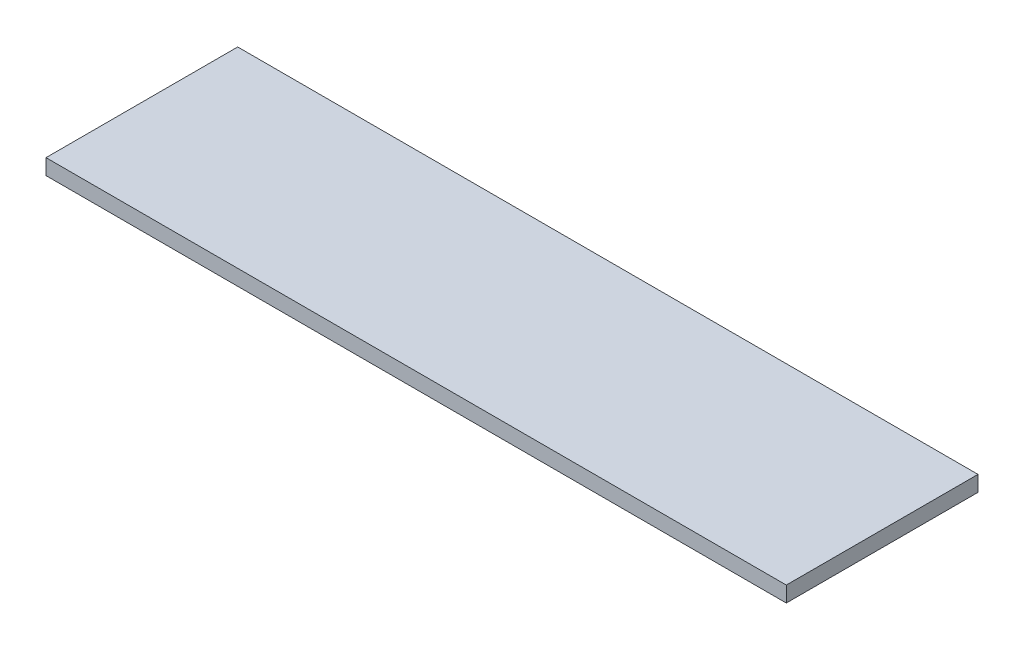
SolidWorks part; units mm, degrees
ref_plane "Front Plane" through (0, 0, 0) normal (0, 0, 1) x (1, 0, 0)
ref_plane "Top Plane" through (0, 0, 0) normal (0, 1, 0) x (1, 0, 0)
ref_plane "Right Plane" through (0, 0, 0) normal (1, 0, 0) x (0, 0, -1)
sketch "Sketch1" plane through (0, 0, 0) normal (0, 1, 0) x (1, 0, 0)
  line L1 (0, 0) -> (47.5, 0)
  line L2 (0, 0) -> (0, 12.3)
  line L3 (0, 12.3) -> (47.5, 12.3)
  line L4 (47.5, 0) -> (47.5, 12.3)
  dimension "D1" = 12.3
  dimension "D2" = 47.5
extrude "Boss-Extrude1" add sketch "Sketch1" along normal blind 1
